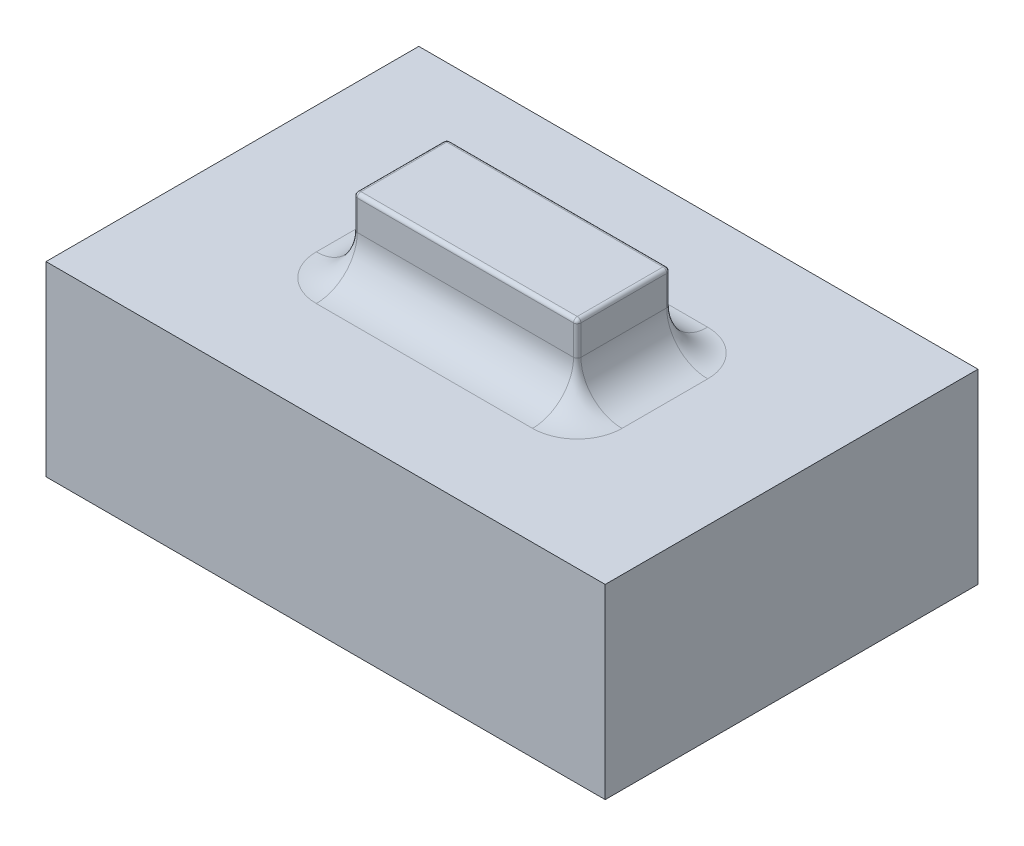
SolidWorks part; units mm, degrees
ref_plane "前视基准面" through (0, 0, 0) normal (0, 0, 1) x (1, 0, 0)
ref_plane "上视基准面" through (0, 0, 0) normal (0, 1, 0) x (1, 0, 0)
ref_plane "右视基准面" through (0, 0, 0) normal (1, 0, 0) x (0, 0, -1)
sketch "草图1" plane through (0, 0, 0) normal (0, 1, 0) x (1, 0, 0)
  line L1 (7.5, 5) -> (-7.5, 5)
  line L2 (7.5, 5) -> (7.5, -5)
  line L3 (7.5, -5) -> (-7.5, -5)
  line L4 (-7.5, 5) -> (-7.5, -5)
  line L5 (7.5, 5) -> (-7.5, -5) construction
  line L6 (7.5, -5) -> (-7.5, 5) construction
  point P0 (0, 0)
  dimension "D1" = 15
  dimension "D2" = 10
extrude "凸台-拉伸1" add sketch "草图1" along normal blind 5
sketch "草图2" plane through (0, 5, 0) normal (0, 1, 0) x (1, 0, 0)
  line L1 (3, 1.25) -> (-3, 1.25)
  line L2 (3, 1.25) -> (3, -1.25)
  line L3 (3, -1.25) -> (-3, -1.25)
  line L4 (-3, 1.25) -> (-3, -1.25)
  line L5 (3, 1.25) -> (-3, -1.25) construction
  line L6 (3, -1.25) -> (-3, 1.25) construction
  point P0 (0, 0)
  dimension "D1" = 6
  dimension "D2" = 2.5
extrude "凸台-拉伸2" add sketch "草图2" along normal blind 2
fillet "圆角1" radius 0.1 4 edges at (-3, 6, -1.25) (3, 6, -1.25) (3, 6, 1.25) (-3, 6, 1.25)
fillet "圆角2" radius 1.1 8 edges at (-2.9707, 5, 1.2207) (-3, 5, 0) (-2.9707, 5, -1.2207) (0, 5, -1.25) (2.9707, 5, -1.2207) (3, 5, 0) (2.9707, 5, 1.2207) (0, 5, 1.25)
fillet "圆角3" radius 0.1 8 edges at (-2.9707, 7, 1.2207) (-3, 7, 0) (-2.9707, 7, -1.2207) (0, 7, -1.25) (2.9707, 7, -1.2207) (3, 7, 0) (2.9707, 7, 1.2207) (0, 7, 1.25)
sketch "方向草图" plane through (0, 5, 0) normal (0, 1, 0) x (1, 0, 0)
  line L0 (2.9, -2.35) -> (-2.9, -2.35) construction
  line L1 (-4.1, -1.15) -> (-4.1, 1.15) construction
  line L2 (-2.9, 2.35) -> (2.9, 2.35) construction
  line L3 (4.1, 1.15) -> (4.1, -1.15) construction
  line L4 (-7.5, 5) -> (-7.5, -5) construction
  line L5 (-7.5, -5) -> (7.5, -5) construction
  line L6 (7.5, -5) -> (7.5, 5) construction
  line L7 (7.5, 5) -> (-7.5, 5) construction
  line L8 (2.9, -2.35) -> (-2.9, -2.35)
  line L9 (-4.1, -1.15) -> (-4.1, 1.15)
  line L10 (-2.9, 2.35) -> (2.9, 2.35)
  line L11 (4.1, 1.15) -> (4.1, -1.15)
  line L12 (-7.5, 5) -> (-7.5, -5) construction
  line L13 (-7.5, -5) -> (7.5, -5) construction
  line L14 (7.5, -5) -> (7.5, 5) construction
  line L15 (7.5, 5) -> (-7.5, 5) construction
  arc A0 (-4.1, -1.15) -> (-2.9, -2.35) centre (-2.9, -1.15) ccw construction
  arc A1 (-2.9, 2.35) -> (-4.1, 1.15) centre (-2.9, 1.15) ccw construction
  arc A2 (4.1, 1.15) -> (2.9, 2.35) centre (2.9, 1.15) ccw construction
  arc A3 (2.9, -2.35) -> (4.1, -1.15) centre (2.9, -1.15) ccw construction
  arc A4 (-4.1, -1.15) -> (-2.9, -2.35) centre (-2.9, -1.15) ccw
  arc A5 (-2.9, 2.35) -> (-4.1, 1.15) centre (-2.9, 1.15) ccw
  arc A6 (4.1, 1.15) -> (2.9, 2.35) centre (2.9, 1.15) ccw
  arc A7 (2.9, -2.35) -> (4.1, -1.15) centre (2.9, -1.15) ccw
  point P14 (0, 0)
other "成形工具1"
